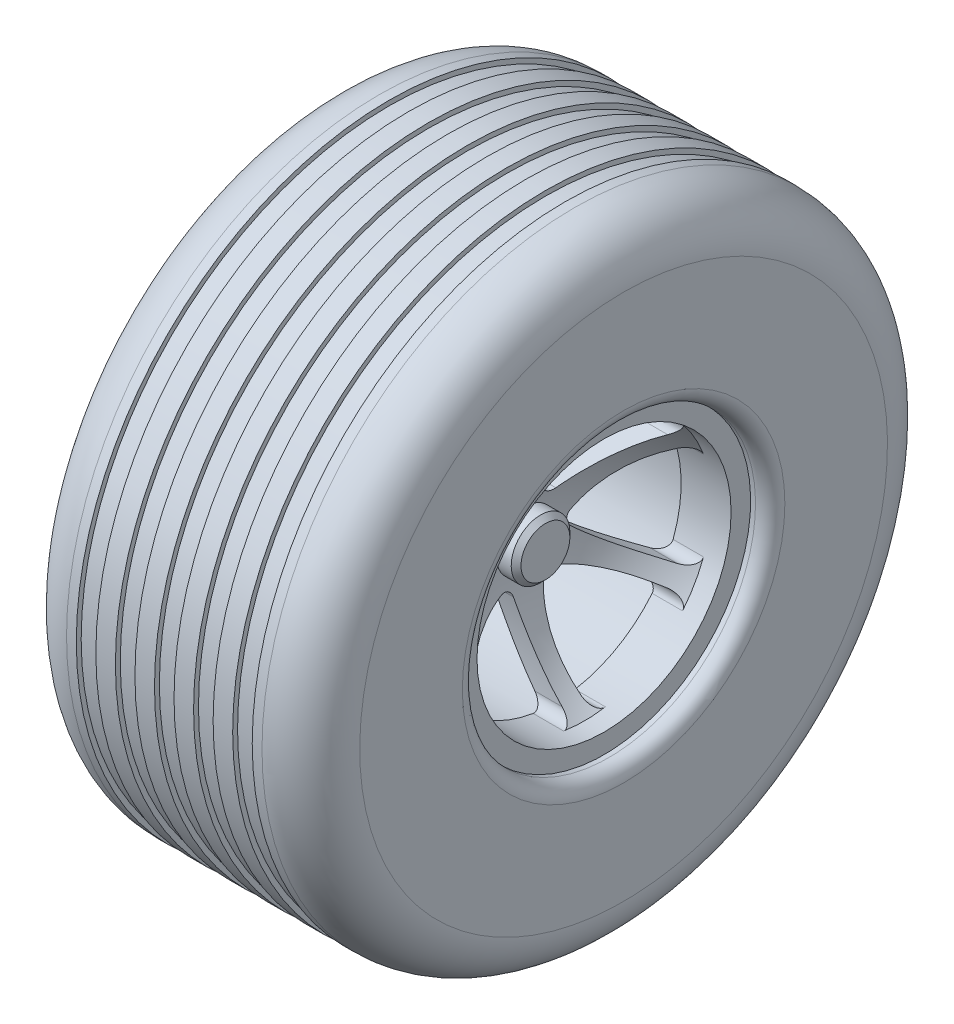
SolidWorks part; units mm, degrees
ref_plane "Front Plane" through (0, 0, 0) normal (0, 0, 1) x (1, 0, 0)
ref_plane "Top Plane" through (0, 0, 0) normal (0, 1, 0) x (1, 0, 0)
ref_plane "Right Plane" through (0, 0, 0) normal (1, 0, 0) x (0, 0, -1)
sketch "Sketch1" plane through (0, 0, 0) normal (0, 0, 1) x (1, 0, 0)
  line L0 (-20, 32) -> (-20, 0) construction
  line L1 (-8, 0) -> (-30, 0)
  line L2 (-13.0998, 3.6239) -> (-11.9316, 3.6239)
  line L3 (-5, 32) -> (-6, 32)
  line L4 (-30, 0) -> (-30, 3)
  line L5 (-30, 3) -> (-15, 3)
  line L6 (-1.5, 15) -> (-2, 15)
  line L7 (-2, 13) -> (-4, 13)
  line L8 (-10, 3) -> (-8, 3)
  line L9 (-26, 13) -> (-28, 13)
  line L10 (0, 13) -> (-30, 13) construction
  line L11 (-30, 16.5) -> (-30, 27)
  line L12 (0, 16.5) -> (0, 27)
  line L13 (-2, 13) -> (-2, 15)
  line L14 (-28, 13) -> (-28, 15)
  line L15 (-28, 15) -> (-28.5, 15)
  line L16 (0, 15) -> (-30, 15) construction
  line L17 (-15, 32) -> (-15, 0) construction
  line L18 (-16, 32) -> (-18, 32)
  line L19 (-12, 31.5) -> (-10, 31.5)
  line L20 (-16, 32) -> (-16, 31.5)
  line L21 (-16, 31.5) -> (-14, 31.5)
  line L22 (-14, 32) -> (-14, 31.5)
  line L23 (-12, 32) -> (-12, 31.5)
  line L24 (-10, 32) -> (-10, 31.5)
  line L25 (-8, 31.5) -> (-6, 31.5)
  line L26 (-8, 32) -> (-8, 31.5)
  line L27 (-6, 32) -> (-6, 31.5)
  line L28 (-18, 31.5) -> (-20, 31.5)
  line L29 (-18, 32) -> (-18, 31.5)
  line L30 (-20, 32) -> (-20, 31.5)
  line L31 (-22, 32) -> (-22, 31.5)
  line L32 (-24, 32) -> (-24, 31.5)
  line L33 (-22, 31.5) -> (-24, 31.5)
  line L34 (-8, 32) -> (-10, 32)
  line L35 (-12, 32) -> (-14, 32)
  line L36 (-20, 32) -> (-22, 32)
  line L37 (-24, 32) -> (-25, 32)
  line L38 (-8, 3) -> (-8, 0)
  line L39 (-5.1609, 14.6286) -> (-24.3429, 14.6286)
  arc A0 (-4, 13) -> (-10, 3) centre (4.4695, 1.1183) ccw
  arc A1 (-26, 13) -> (-15, 3) centre (-29.3199, -1.7019) cw
  arc A2 (-1.5, 15) -> (0, 16.5) centre (-1.5, 16.5) ccw
  arc A3 (-28.5, 15) -> (-30, 16.5) centre (-28.5, 16.5) cw
  arc A4 (0, 27) -> (-5, 32) centre (-5, 27) ccw
  arc A5 (-25, 32) -> (-30, 27) centre (-25, 27) ccw
  arc A6 (-5.1609, 14.6286) -> (-11.9316, 3.6239) centre (4.4695, 1.1183) ccw
  arc A7 (-24.3429, 14.6286) -> (-13.0998, 3.6239) centre (-29.3199, -1.7019) cw
  arc A8 (-25.5595, 14.9509) -> (-13.0998, 3.6239) centre (-29.3199, -1.7019) cw construction
  arc A9 (-5.1609, 14.6286) -> (-11.9833, 3.2579) centre (4.4695, 1.1183) ccw construction
  point P13 (-4, 13)
  point P14 (-10, 3)
  point P18 (-26, 13)
  point P19 (-15, 3)
  point P35 (0, 32)
  point P38 (-30, 32)
  dimension "D5" = 5
  dimension "D1" = 32
  dimension "D2" = 30
  dimension "D3" = 10
  dimension "D4" = 2
  dimension "D7" = 0.5
  dimension "D8" = 2
  dimension "D9" = 2
  dimension "D10" = 2
  dimension "D6" = 2
revolve "Revolve1" add sketch "Sketch1" angle 360 about L1
chamfer "Chamfer1" distance 0.5 angle 45 1 edges at (-8, 3, 0)
sketch "Sketch2" plane through (-2, 0, 0) normal (1, 0, 0) x (0, 0, -1)
  line L0 (0, 15) -> (0, -15) construction
  line L1 (1.2429, 2.7304) -> (1.246, 2.7373)
  line L2 (-15, 0) -> (15, 0) construction
  line L3 (2.8988, 6.368) -> (2.9001, 6.371)
  arc A0 (-2.1435, 12.8221) -> (-10.0325, 8.2674) centre (0, 0) ccw
  arc A1 (2.8106, 3.3839) -> (1.5252, 4.126) centre (2.503, 4.3354) cw
  circle A2 centre (0, 0) radius 15 construction
  arc A3 (-0.9812, 11.9071) -> (-1.5252, 4.126) centre (-28.63, 9.9307) cw
  arc A4 (0.9812, 11.9071) -> (1.5252, 4.126) centre (28.63, 9.9307) ccw
  arc A5 (9.8212, 6.8032) -> (2.8106, 3.3839) centre (-5.7148, 29.7597) cw
  arc A6 (10.8024, 5.1038) -> (4.3358, 0.7421) centre (22.9152, -19.829) ccw
  arc A7 (10.8024, -5.1038) -> (4.3358, -0.7421) centre (22.9152, 19.829) cw
  arc A8 (9.8212, -6.8032) -> (2.8106, -3.3839) centre (-5.7148, -29.7597) ccw
  arc A9 (0.9812, -11.9071) -> (1.5252, -4.126) centre (28.63, -9.9307) cw
  arc A10 (-0.9812, -11.9071) -> (-1.5252, -4.126) centre (-28.63, -9.9307) ccw
  arc A11 (-9.8212, -6.8032) -> (-2.8106, -3.3839) centre (5.7148, -29.7597) cw
  arc A12 (-10.8024, -5.1038) -> (-4.3358, -0.7421) centre (-22.9152, 19.829) ccw
  arc A13 (-10.8024, 5.1038) -> (-4.3358, 0.7421) centre (-22.9152, -19.829) cw
  arc A14 (-9.8212, 6.8032) -> (-2.8106, 3.3839) centre (5.7148, 29.7597) ccw
  arc A15 (-12.176, 4.5547) -> (-12.176, -4.5547) centre (0, 0) ccw
  arc A16 (-10.0325, -8.2674) -> (-2.1435, -12.8221) centre (0, 0) ccw
  arc A17 (2.1435, -12.8221) -> (10.0325, -8.2674) centre (0, 0) ccw
  arc A18 (12.176, -4.5547) -> (12.176, 4.5547) centre (0, 0) ccw
  arc A19 (10.0325, 8.2674) -> (2.1435, 12.8221) centre (0, 0) ccw
  arc A20 (4.3358, -0.7421) -> (4.3358, 0.7421) centre (5.0061, 0) cw
  arc A21 (1.5252, -4.126) -> (2.8106, -3.3839) centre (2.503, -4.3354) cw
  arc A22 (-2.8106, -3.3839) -> (-1.5252, -4.126) centre (-2.503, -4.3354) cw
  arc A23 (-4.3358, 0.7421) -> (-4.3358, -0.7421) centre (-5.0061, 0) cw
  arc A24 (-1.5252, 4.126) -> (-2.8106, 3.3839) centre (-2.503, 4.3354) cw
  arc A25 (0.9812, 11.9071) -> (2.1435, 12.8221) centre (1.9786, 11.8358) cw
  arc A26 (9.8212, 6.8032) -> (10.0325, 8.2674) centre (9.2607, 7.6314) ccw
  arc A27 (10.8024, 5.1038) -> (12.176, 4.5547) centre (11.2394, 4.2043) cw
  arc A28 (10.8024, -5.1038) -> (12.176, -4.5547) centre (11.2394, -4.2043) ccw
  arc A29 (9.8212, -6.8032) -> (10.0325, -8.2674) centre (9.2607, -7.6314) cw
  arc A30 (0.9812, -11.9071) -> (2.1435, -12.8221) centre (1.9786, -11.8358) ccw
  arc A31 (-0.9812, -11.9071) -> (-2.1435, -12.8221) centre (-1.9786, -11.8358) cw
  arc A32 (-9.8212, -6.8032) -> (-10.0325, -8.2674) centre (-9.2607, -7.6314) ccw
  arc A33 (-10.8024, -5.1038) -> (-12.176, -4.5547) centre (-11.2394, -4.2043) cw
  arc A34 (-10.8024, 5.1038) -> (-12.176, 4.5547) centre (-11.2394, 4.2043) ccw
  arc A35 (-9.8212, 6.8032) -> (-10.0325, 8.2674) centre (-9.2607, 7.6314) cw
  arc A36 (-0.9812, 11.9071) -> (-2.1435, 12.8221) centre (-1.9786, 11.8358) ccw
  point P37 (3.5458, 0)
  point P54 (-3.5458, 0)
  point P59 (1.0761, 12.9554)
  point P82 (-1.0761, 12.9554)
  dimension "D1" = 1
  dimension "D2" = 1
extrude "Cut-Extrude2" cut sketch "Sketch2" against normal blind 40
